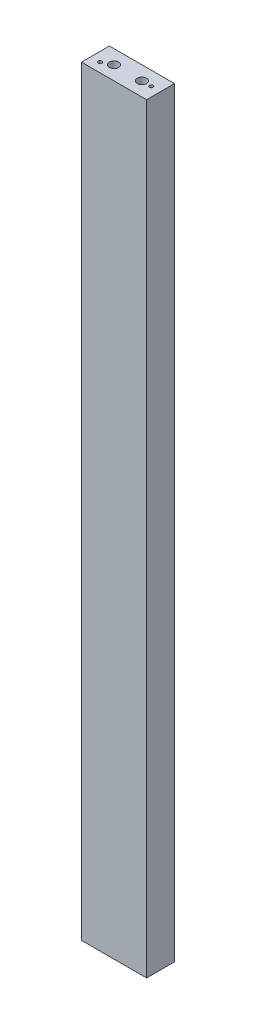
SolidWorks part; units mm, degrees
ref_plane "Front Plane" through (0, 0, 0) normal (0, 0, 1) x (1, 0, 0)
ref_plane "Top Plane" through (0, 0, 0) normal (0, 1, 0) x (1, 0, 0)
ref_plane "Right Plane" through (0, 0, 0) normal (1, 0, 0) x (0, 0, -1)
sketch "Sketch1" plane through (0, 0, 0) normal (0, 1, 0) x (1, 0, 0)
  line L1 (0, 0) -> (88.9, 0)
  line L2 (0, 0) -> (0, -38.1)
  line L3 (0, -38.1) -> (88.9, -38.1)
  line L4 (88.9, 0) -> (88.9, -38.1)
  dimension "D1" = 38.1
  dimension "D2" = 88.9
extrude "Boss-Extrude1" add sketch "Sketch1" along normal blind 1038.225
sketch "Sketch2" plane through (0, 1038.225, 0) normal (0, 1, 0) x (1, 0, 0)
  line L0 (0, 0) -> (0, -38.1) construction
  line L1 (25.4, -19.05) -> (63.5, -19.05) construction
  line L2 (88.9, 0) -> (0, 0) construction
  circle A0 centre (25.4, -19.05) radius 6.35
  circle A1 centre (63.5, -19.05) radius 6.35
  point P7 (0, -19.05)
  point P9 (44.45, 0)
  point P10 (44.45, -19.05)
  dimension "D1" = 12.7
  dimension "D2" = 12.7
  dimension "D3" = 38.1
extrude "Cut-Extrude1" cut sketch "Sketch2" against normal blind 19.05
sketch "Sketch3" plane through (0, 0, 0) normal (0, -1, 0) x (1, 0, 0)
  line L0 (25.4, 19.05) -> (63.5, 19.05) construction
  line L1 (0, 38.1) -> (88.9, 38.1) construction
  line L2 (0, 0) -> (0, 38.1) construction
  circle A0 centre (25.4, 19.05) radius 6.35
  circle A1 centre (63.5, 19.05) radius 6.35
  point P6 (44.45, 38.1)
  point P7 (44.45, 19.05)
  point P10 (0, 19.05)
  dimension "D1" = 12.7
  dimension "D2" = 12.7
  dimension "D3" = 38.1
extrude "Cut-Extrude2" cut sketch "Sketch3" against normal blind 19.05
sketch "Sketch4" plane through (0, 1038.225, 0) normal (0, 1, 0) x (1, 0, 0)
  line L0 (88.9, -38.1) -> (88.9, 0) construction
  line L1 (88.9, 0) -> (0, 0) construction
  point P0 (12.7, -25.4)
  point P1 (76.2, -19.05)
  dimension "D1" = 76.2
  dimension "D2" = 12.7
  dimension "D3" = 19.05
  dimension "D4" = 25.4
sketch "Sketch5" plane through (0, 0, 0) normal (0, -1, 0) x (1, 0, 0)
  line L0 (0, 0) -> (0, 38.1) construction
  line L1 (88.9, 0) -> (0, 0) construction
  point P0 (44.45, 25.4)
  dimension "D1" = 44.45
  dimension "D2" = 25.4
hole_wizard "#10 (0.1935) Diameter Hole1" positions "3DSketch1" profile "Sketch6" hole size "#10" standard "ANSI Inch"
sketch3d "3DSketch1"
  point P0 (44.45, 0, 25.4)
  point P3 (12.7, 1038.225, 25.4)
  point P6 (76.2, 1038.225, 19.05)
sketch "Sketch6" plane through (44.45, 0, 25.4) normal (1, 0, 0) x (0, 0, -1)
  line L0 (0, 0) -> (0, 77.6766)
  line L1 (0, 77.6766) -> (2.4574, 76.2)
  line L2 (2.4574, 76.2) -> (2.4574, 0)
  line L5 (2.4574, 0) -> (0, 0)
  line L10 (0, 77.6766) -> (-2.4575, 76.2) construction
  line L11 (0, -6.35) -> (0, 107.95) construction
  dimension "Hole Dia." = 4.9149
  dimension "Hole Depth" = 76.2
  dimension "Drill Angle" = 118
